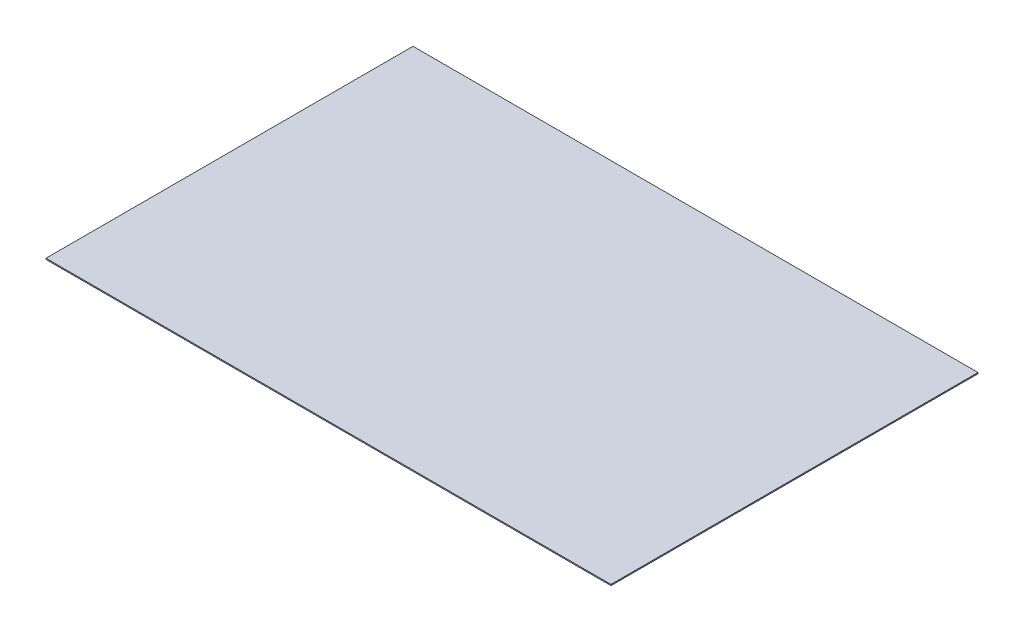
SolidWorks part; units mm, degrees
ref_plane "Front Plane" through (0, 0, 0) normal (0, 0, 1) x (1, 0, 0)
ref_plane "Top Plane" through (0, 0, 0) normal (0, 1, 0) x (1, 0, 0)
ref_plane "Right Plane" through (0, 0, 0) normal (1, 0, 0) x (0, 0, -1)
sketch "Sketch1" plane through (0, 0, 0) normal (0, 1, 0) x (1, 0, 0)
  line L1 (0, 0) -> (809.752, 0)
  line L2 (0, 0) -> (0, 526.034)
  line L3 (0, 526.034) -> (809.752, 526.034)
  line L4 (809.752, 0) -> (809.752, 526.034)
  dimension "D1" = 526.034
  dimension "D2" = 809.752
extrude "Boss-Extrude1" add sketch "Sketch1" along normal blind 1.5875
